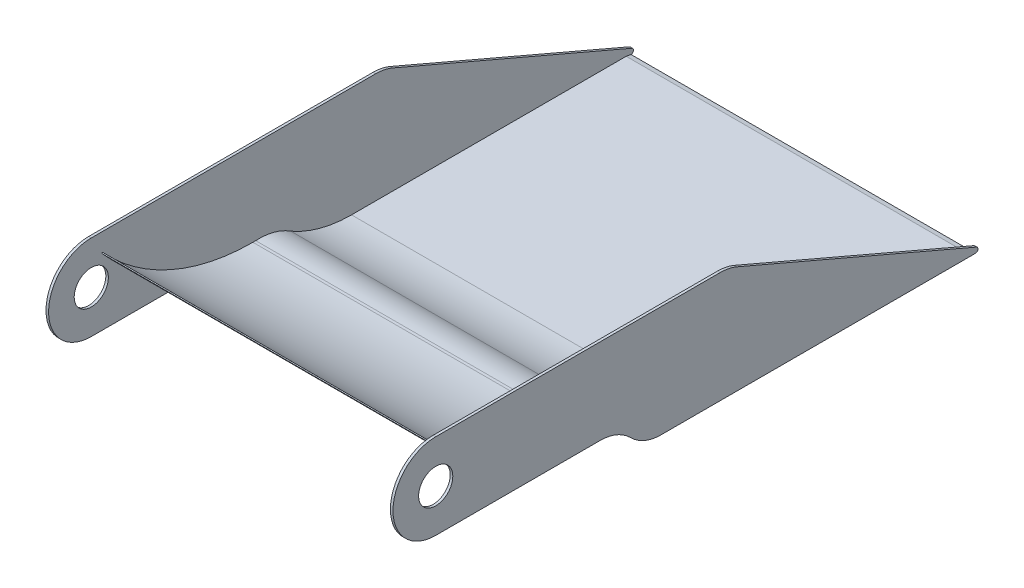
SolidWorks part; units mm, degrees
ref_plane "前视基准面" through (0, 0, 0) normal (0, 0, 1) x (1, 0, 0)
ref_plane "上视基准面" through (0, 0, 0) normal (0, 1, 0) x (1, 0, 0)
ref_plane "右视基准面" through (0, 0, 0) normal (1, 0, 0) x (0, 0, -1)
sketch "草图1" plane through (0, 0, 0) normal (1, 0, 0) x (0, 0, -1)
  line L0 (0, -50) -> (192.4171, -50)
  line L1 (227.7725, -64.6447) -> (228.4052, -65.2773)
  line L2 (263.7605, -79.922) -> (631.5408, -79.922)
  line L3 (0, 50) -> (332.7855, 50)
  line L4 (352.484, 45.9562) -> (632.7227, -74.1646)
  circle A0 centre (0, 0) radius 20
  circle A1 centre (0, 0) radius 50
  arc A2 (632.7227, -74.1646) -> (631.5408, -79.922) centre (631.5408, -76.922) cw
  arc A3 (192.4171, -50) -> (227.7725, -64.6447) centre (192.4171, -100) cw
  arc A4 (228.4052, -65.2773) -> (263.7605, -79.922) centre (263.7605, -29.922) ccw
  arc A5 (332.7855, 50) -> (352.484, 45.9562) centre (332.7855, 0) cw
  point P10 (640.2328, -79.922)
  dimension "D1" = 3
  dimension "D2" = 50
  dimension "D3" = 50
extrude "凸台-拉伸1" add sketch "草图1" along normal blind 3 contours A5 L3 A1 L0 A3 L1 A4 L2 A2 L4 | A1 A0
sketch "草图2" plane through (0, 0, 0) normal (-1, 0, 0) x (0, 0, 1)
  line L0 (-304.4948, -78.922) -> (-625.8695, -78.922)
  line L1 (-625.8695, -78.922) -> (-631.5408, -79.922)
  line L2 (-192.4171, -49) -> (-189.1043, -49)
  line L5 (-352.484, 45.9562) -> (-632.7227, -74.1646)
  line L6 (-631.5408, -79.922) -> (-263.7605, -79.922)
  line L7 (-228.4052, -65.2773) -> (-227.7725, -64.6447)
  line L8 (-192.4171, -50) -> (0, -50)
  line L9 (0, 50) -> (-332.7855, 50)
  line L10 (-352.484, 45.9562) -> (-632.7227, -74.1646)
  line L11 (-631.5408, -79.922) -> (-263.7605, -79.922)
  line L12 (-228.4052, -65.2773) -> (-227.7725, -64.6447)
  line L13 (-192.4171, -50) -> (0, -50)
  line L14 (0, 50) -> (-332.7855, 50)
  arc A0 (-189.1043, -49) -> (-13.5824, 28.4189) centre (-189.1043, 188.6786) ccw
  arc A1 (-304.4948, -78.922) -> (-233.6064, -60.0158) centre (-304.4948, 63.4285) ccw
  arc A2 (-233.6064, -60.0158) -> (-192.4171, -49) centre (-196.5294, -116.1371) cw
  arc A3 (-170.7649, -50) -> (-12.213, 28.1962) centre (-186.4028, 181.5469) ccw
  arc A4 (-13.5824, 28.4189) -> (-12.213, 28.1962) centre (-12.9765, 27.8228) cw
  arc A5 (-332.7855, 50) -> (-352.484, 45.9562) centre (-332.7855, 0) ccw
  arc A6 (-632.7227, -74.1646) -> (-631.5408, -79.922) centre (-631.5408, -76.922) ccw
  arc A7 (-263.7605, -79.922) -> (-228.4052, -65.2773) centre (-263.7605, -29.922) ccw
  arc A8 (-192.4171, -50) -> (-227.7725, -64.6447) centre (-192.4171, -100) ccw
  arc A9 (0, -50) -> (0, 50) centre (0, 0) ccw
  arc A10 (-332.7855, 50) -> (-352.484, 45.9562) centre (-332.7855, 0) ccw
  arc A11 (-632.7227, -74.1646) -> (-631.5408, -79.922) centre (-631.5408, -76.922) ccw
  arc A12 (-263.7605, -79.922) -> (-228.4052, -65.2773) centre (-263.7605, -29.922) ccw
  arc A13 (-192.4171, -50) -> (-227.7725, -64.6447) centre (-192.4171, -100) ccw
  arc A14 (0, -50) -> (0, 50) centre (0, 0) ccw
  point P0 (-304.4948, -78.922)
  point P10 (-192.4171, -49)
  point P29 (-13.5824, 28.4189)
  line M19 (-631.5408, -79.922) -> (-263.7605, -79.922)
  arc M20 (-263.7605, -79.922) -> (-228.4052, -65.2773) centre (-263.7605, -29.922) ccw
  line M21 (-228.4052, -65.2773) -> (-227.7725, -64.6447)
  arc M22 (-227.7725, -64.6447) -> (-192.4171, -50) centre (-192.4171, -100) cw
  line M23 (-192.4171, -50) -> (0, -50)
  dimension "D2" = 1
  dimension "D3" = 1
  dimension "D4" = 10
  dimension "D1" = 0
extrude "凸台-拉伸2" add sketch "草图2" along normal blind 400 contours A4 A0 L2 A2 A1 L0 L1 A3 M19 M20 M21 M22 M23
sketch "草图3" plane through (-400, 0, 0) normal (-1, 0, 0) x (0, 0, 1)
  line L6 (-170.7649, -50) -> (0, -50)
  line L7 (0, 50) -> (-332.7855, 50)
  line L8 (-352.484, 45.9562) -> (-632.7227, -74.1646)
  line L9 (-631.5408, -79.922) -> (-625.8695, -78.922)
  line L10 (-625.8695, -78.922) -> (-304.4948, -78.922)
  line L11 (-192.4171, -49) -> (-189.1043, -49)
  line L12 (-170.7649, -50) -> (0, -50)
  line L13 (0, 50) -> (-332.7855, 50)
  line L14 (-352.484, 45.9562) -> (-632.7227, -74.1646)
  line L15 (-631.5408, -79.922) -> (-625.8695, -78.922)
  line L16 (-625.8695, -78.922) -> (-304.4948, -78.922)
  line L17 (-192.4171, -49) -> (-189.1043, -49)
  line L18 (-189.1043, -49) -> (-192.4171, -49)
  line L19 (-304.4948, -78.922) -> (-625.8695, -78.922)
  line L20 (-625.8695, -78.922) -> (-631.5408, -79.922)
  line L21 (-631.5408, -79.922) -> (-263.7605, -79.922)
  line L22 (-228.4052, -65.2773) -> (-227.7725, -64.6447)
  line L23 (-192.4171, -50) -> (-170.7649, -50)
  line L24 (-189.1043, -49) -> (-192.4171, -49)
  line L25 (-304.4948, -78.922) -> (-625.8695, -78.922)
  line L26 (-625.8695, -78.922) -> (-631.5408, -79.922)
  line L27 (-631.5408, -79.922) -> (-263.7605, -79.922)
  line L28 (-228.4052, -65.2773) -> (-227.7725, -64.6447)
  line L29 (-192.4171, -50) -> (-170.7649, -50)
  circle A0 centre (0, 0) radius 20 construction
  circle A1 centre (0, 0) radius 20
  arc A7 (-12.213, 28.1962) -> (-13.5824, 28.4189) centre (-12.9765, 27.8228) ccw
  arc A8 (-170.7649, -50) -> (-12.213, 28.1962) centre (-186.4028, 181.5469) ccw
  arc A9 (0, -50) -> (0, 50) centre (0, 0) ccw
  arc A10 (-332.7855, 50) -> (-352.484, 45.9562) centre (-332.7855, 0) ccw
  arc A11 (-632.7227, -74.1646) -> (-631.5408, -79.922) centre (-631.5408, -76.922) ccw
  arc A12 (-304.4948, -78.922) -> (-233.6064, -60.0158) centre (-304.4948, 63.4285) ccw
  arc A13 (-192.4171, -49) -> (-233.6064, -60.0158) centre (-196.5294, -116.1371) ccw
  arc A14 (-189.1043, -49) -> (-13.5824, 28.4189) centre (-189.1043, 188.6786) ccw
  arc A15 (-12.213, 28.1962) -> (-13.5824, 28.4189) centre (-12.9765, 27.8228) ccw
  arc A16 (-170.7649, -50) -> (-12.213, 28.1962) centre (-186.4028, 181.5469) ccw
  arc A17 (0, -50) -> (0, 50) centre (0, 0) ccw
  arc A18 (-332.7855, 50) -> (-352.484, 45.9562) centre (-332.7855, 0) ccw
  arc A19 (-632.7227, -74.1646) -> (-631.5408, -79.922) centre (-631.5408, -76.922) ccw
  arc A20 (-304.4948, -78.922) -> (-233.6064, -60.0158) centre (-304.4948, 63.4285) ccw
  arc A21 (-192.4171, -49) -> (-233.6064, -60.0158) centre (-196.5294, -116.1371) ccw
  arc A22 (-189.1043, -49) -> (-13.5824, 28.4189) centre (-189.1043, 188.6786) ccw
  arc A23 (-12.213, 28.1962) -> (-13.5824, 28.4189) centre (-12.9765, 27.8228) ccw
  arc A24 (-189.1043, -49) -> (-13.5824, 28.4189) centre (-189.1043, 188.6786) ccw
  arc A25 (-192.4171, -49) -> (-233.6064, -60.0158) centre (-196.5294, -116.1371) ccw
  arc A26 (-304.4948, -78.922) -> (-233.6064, -60.0158) centre (-304.4948, 63.4285) ccw
  arc A27 (-263.7605, -79.922) -> (-228.4052, -65.2773) centre (-263.7605, -29.922) ccw
  arc A28 (-192.4171, -50) -> (-227.7725, -64.6447) centre (-192.4171, -100) ccw
  arc A29 (-170.7649, -50) -> (-12.213, 28.1962) centre (-186.4028, 181.5469) ccw
  arc A30 (-12.213, 28.1962) -> (-13.5824, 28.4189) centre (-12.9765, 27.8228) ccw
  arc A31 (-189.1043, -49) -> (-13.5824, 28.4189) centre (-189.1043, 188.6786) ccw
  arc A32 (-192.4171, -49) -> (-233.6064, -60.0158) centre (-196.5294, -116.1371) ccw
  arc A33 (-304.4948, -78.922) -> (-233.6064, -60.0158) centre (-304.4948, 63.4285) ccw
  arc A34 (-263.7605, -79.922) -> (-228.4052, -65.2773) centre (-263.7605, -29.922) ccw
  arc A35 (-192.4171, -50) -> (-227.7725, -64.6447) centre (-192.4171, -100) ccw
  arc A36 (-170.7649, -50) -> (-12.213, 28.1962) centre (-186.4028, 181.5469) ccw
  arc M28 (-12.213, 28.1962) -> (-13.5824, 28.4189) centre (-12.9765, 27.8228) ccw
  arc M29 (-13.5824, 28.4189) -> (-189.1043, -49) centre (-189.1043, 188.6786) cw
  line M30 (-189.1043, -49) -> (-192.4171, -49)
  arc M31 (-192.4171, -49) -> (-233.6064, -60.0158) centre (-196.5294, -116.1371) ccw
  arc M32 (-233.6064, -60.0158) -> (-304.4948, -78.922) centre (-304.4948, 63.4285) cw
  line M33 (-304.4948, -78.922) -> (-625.8695, -78.922)
  line M34 (-625.8695, -78.922) -> (-631.5408, -79.922)
  line M35 (-631.5408, -79.922) -> (-263.7605, -79.922)
  arc M36 (-263.7605, -79.922) -> (-228.4052, -65.2773) centre (-263.7605, -29.922) ccw
  line M37 (-228.4052, -65.2773) -> (-227.7725, -64.6447)
  arc M38 (-227.7725, -64.6447) -> (-192.4171, -50) centre (-192.4171, -100) cw
  line M39 (-192.4171, -50) -> (-170.7649, -50)
  arc M40 (-170.7649, -50) -> (-12.213, 28.1962) centre (-186.4028, 181.5469) ccw
  dimension "D1" = 0
  dimension "D2" = 0
extrude "凸台-拉伸3" add sketch "草图3" along normal blind 3 contours L14 A19 L12 A17 L13 A18 A1 M34 M33 M32 M31 M30 M29 M28 M40 | M40 M28 M29 M30 M31 M32 M33 M34 M35 M36 M37 M38 M39
